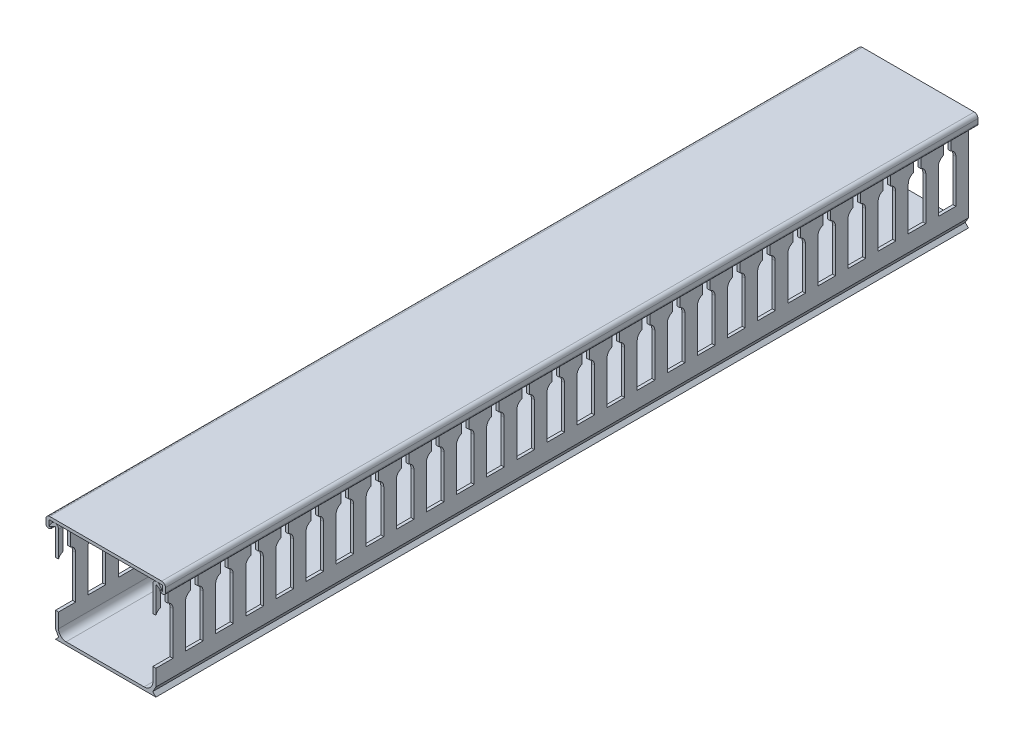
SolidWorks part; units mm, degrees
ref_plane "Front Plane" through (0, 0, 0) normal (0, 0, 1) x (1, 0, 0)
ref_plane "Top Plane" through (0, 0, 0) normal (0, 1, 0) x (1, 0, 0)
ref_plane "Right Plane" through (0, 0, 0) normal (1, 0, 0) x (0, 0, -1)
sketch "Sketch1" plane through (0, 0, 0) normal (0, 0, 1) x (1, 0, 0)
  line L0 (-20, 0) -> (20, 0)
  line L1 (-20, 3.5) -> (-20, 38.546)
  line L2 (-20, 0) -> (-18.7189, 1.2811)
  line L3 (-18.7189, 1.2811) -> (-20, 3.5)
  line L4 (-22.4196, 37.589) -> (-20.381, 38.766)
  line L5 (0, 0) -> (0, -17.0643) construction
  line L6 (22.4196, 37.589) -> (22.5, 37.889)
  line L7 (22.4196, 37.589) -> (20.381, 38.766)
  line L8 (20, 3.5) -> (20, 38.546)
  line L9 (18.7189, 1.2811) -> (20, 3.5)
  line L10 (-22.4196, 37.589) -> (-22.5, 37.889)
  line L11 (20, 0) -> (18.7189, 1.2811)
  line L12 (-18.8, 4.2) -> (-18.8, 38.546)
  line L13 (18.8, 3.5) -> (18.8, 38.546) construction
  line L14 (-17.2865, 1.2) -> (20, 1.2) construction
  line L15 (-15.8, 1.2) -> (15.3, 1.2)
  line L16 (18.8, 4.7) -> (18.8, 38.546)
  line L17 (-17.2865, 1.2) -> (-18.8, 3.8215) construction
  line L18 (-17.2865, 1.2) -> (-17.2865, 1.2) construction
  line L19 (-18.8, 3.8215) -> (-18.8, 38.546) construction
  arc A0 (-22.5, 37.889) -> (-21.2623, 39.5936) centre (-17.1014, 35.2708) cw
  arc A1 (22.5, 37.889) -> (21.2623, 39.5936) centre (17.1014, 35.2708) ccw
  arc A2 (20.381, 38.766) -> (20, 38.546) centre (20.254, 38.546) ccw
  arc A3 (-21.2623, 39.5936) -> (-18.8, 38.546) centre (-20.254, 38.546) cw
  arc A4 (21.2623, 39.5936) -> (18.8, 38.546) centre (20.254, 38.546) ccw
  arc A5 (-15.8, 1.2) -> (-18.8, 4.2) centre (-15.8, 4.2) cw
  arc A6 (-20.381, 38.766) -> (-20, 38.546) centre (-20.254, 38.546) cw
  arc A7 (15.3, 1.2) -> (18.8, 4.7) centre (15.3, 4.7) ccw
  arc A8 (-20.981, 39.8052) -> (-18.8, 38.546) centre (-20.254, 38.546) cw construction
  arc A9 (20.981, 39.8052) -> (18.8, 38.546) centre (20.254, 38.546) ccw construction
  dimension "D1" = 0.3
  dimension "D2" = 6
  dimension "D3" = 60
  dimension "D5" = 0.254
  dimension "D6" = 1.2
  dimension "D11" = 3
  dimension "D13" = 3.5
  dimension "D14" = 40
  dimension "D7" = 45
  dimension "D8" = 30
  dimension "D4" = 75
  dimension "D9" = 3.5
  dimension "D10" = 2.5
  dimension "D12" = 40
extrude "Boss-Extrude2" add sketch "Sketch1" along normal mid plane 1000 contours L0 L11 L9 L8 A2 L7 L6 A1 A4 L16 A7 L15 A5 L12 A3 A0 L10 L4 A6 L1 L3 L2
sketch "Sketch2" plane through (0, 0, 0) normal (1, 0, 0) x (0, 0, -1)
  line L0 (490, 30) -> (490, 40)
  line L1 (-500, 0) -> (500, 0) construction
  line L2 (500, 3.5) -> (500, 38.546) construction
  line L3 (488, 10) -> (495, 10)
  line L4 (495, 10) -> (495, 27.1716)
  line L6 (490, 40) -> (493, 40)
  line L7 (493, 30) -> (493, 40)
  line L8 (488, 10) -> (488, 27.1716)
  line L10 (500, 40) -> (-500, 40) construction
  arc A0 (495, 27.1716) -> (493, 30) centre (492, 27.1716) ccw
  arc A1 (488, 27.1716) -> (490, 30) centre (491, 27.1716) cw
  point P22 (491.5, 10)
  point P23 (491.5, 40)
  dimension "D1" = 3
  dimension "D2" = 10
  dimension "D3" = 10
  dimension "D4" = 7
  dimension "D5" = 5
  dimension "D6" = 3
extrude "Cut-Extrude1" cut sketch "Sketch2" against normal blind 82.296 and the other way blind 151.13
pattern_linear "LPattern1" count 83 spacing 12 along (0, 0, 1) of "Cut-Extrude1"
sketch "Sketch3" plane through (0, 0, -500) normal (0, 0, 1) x (1, 0, 0)
  line L0 (-22.6, 37.9) -> (-22.6, 39.7) construction
  line L1 (-22.6, 37.8781) -> (-22.6, 39.7)
  line L2 (22.3, 40) -> (-22.3, 40)
  line L4 (22.6, 37.8781) -> (22.6, 39.7)
  line L5 (22.6, 37.9) -> (22.6, 39.7) construction
  line L6 (22.3, 41.2) -> (-22.3, 41.2)
  line L7 (-22.3, 37.034) -> (-21.6, 37.4381)
  line L8 (-21.6, 37.4381) -> (-21.6, 38.0155)
  line L9 (-23.8, 37.9) -> (-23.8, 39.7)
  line L10 (-21.6, 38.0155) -> (-22.219, 37.6581)
  line L12 (22.3, 37.034) -> (21.6, 37.4381)
  line L14 (21.6, 38.0155) -> (22.219, 37.6581)
  line L15 (23.8, 37.9) -> (23.8, 39.7)
  line L16 (21.6, 37.4381) -> (21.6, 38.0155)
  arc A0 (-23.8, 37.9) -> (-22.3, 37.034) centre (-22.8, 37.9) ccw
  arc A1 (-22.6, 37.8781) -> (-22.219, 37.6581) centre (-22.346, 37.8781) ccw
  arc A2 (22.3, 37.034) -> (23.8, 37.9) centre (22.8, 37.9) ccw
  arc A3 (-22.3, 41.2) -> (-23.8, 39.7) centre (-22.3, 39.7) ccw
  arc A4 (-22.3, 40) -> (-22.6, 39.7) centre (-22.3, 39.7) ccw
  arc A5 (22.3, 41.2) -> (23.8, 39.7) centre (22.3, 39.7) cw
  arc A6 (22.3, 40) -> (22.6, 39.7) centre (22.3, 39.7) cw
  arc A7 (22.6, 37.8781) -> (22.219, 37.6581) centre (22.346, 37.8781) cw
  arc A9 (-18.8, 38.546) -> (-21.2623, 39.5936) centre (-20.254, 38.546) ccw construction
  point P35 (0, 40)
  dimension "D2" = 2.2
  dimension "D3" = 0.254
  dimension "D4" = 2.2
  dimension "D5" = 1.5
  dimension "D7" = 4.3
  dimension "D12" = 1
  dimension "D6" = 60
  dimension "D8" = 60
  dimension "D9" = 0.5
  dimension "D11" = 0.1
  dimension "D10" = 1.2
extrude "Boss-Extrude3" add sketch "Sketch3" along normal up to vertex separate body
sketch "Sketch4" plane through (0, 0, 500) normal (0, 0, 1) x (1, 0, 0)
  line L1 (-26.5388, 43.9432) -> (25.6964, 43.9432)
  line L2 (-26.5388, 43.9432) -> (-26.5388, -2.0778)
  line L3 (-26.5388, -2.0778) -> (25.6964, -2.0778)
  line L4 (25.6964, 43.9432) -> (25.6964, -2.0778)
extrude "Cut-Extrude2" cut sketch "Sketch4" against normal blind 676.2
